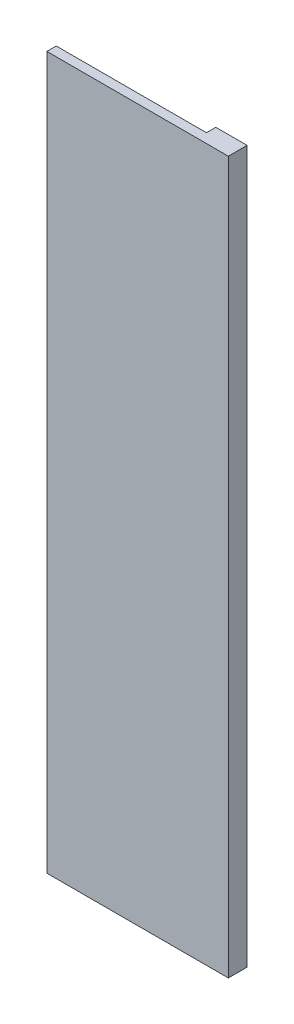
SolidWorks part; units mm, degrees
ref_plane "Front Plane" through (0, 0, 0) normal (0, 0, 1) x (1, 0, 0)
ref_plane "Top Plane" through (0, 0, 0) normal (0, 1, 0) x (1, 0, 0)
ref_plane "Right Plane" through (0, 0, 0) normal (1, 0, 0) x (0, 0, -1)
sketch "Sketch1" plane through (0, 0, 0) normal (0, 0, 1) x (1, 0, 0)
  line L0 (-48, 0) -> (48, 0) construction
  line L1 (-48, 435) -> (68, 435)
  line L2 (-48, 435) -> (-48, -20)
  line L3 (-48, -20) -> (68, -20)
  line L4 (68, 435) -> (68, -20)
  line L5 (48, 435) -> (48, 0) construction
  line L7 (48, 435) -> (-48, 435)
  line L8 (48, 435) -> (48, 0)
  line L9 (48, 0) -> (-48, 0)
  line L10 (-48, 435) -> (-48, 0)
  dimension "D1" = 20
  dimension "D2" = 20
extrude "Boss-Extrude1" add sketch "Sketch1" against normal blind 6 contours L8 L9 L2 L3 L4 L1
sketch "Sketch2" plane through (0, 0, 0) normal (0, 0, 1) x (1, 0, 0)
  line L1 (68, -20) -> (-48, -20)
  line L2 (68, -20) -> (68, 435)
  line L3 (68, 435) -> (-48, 435)
  line L4 (-48, -20) -> (-48, 435)
extrude "Boss-Extrude2" add sketch "Sketch2" along normal blind 6
sketch "Sketch3" plane through (0, 0, -6) normal (0, 0, -1) x (-1, 0, 0)
  circle A0 centre (-48, 0) radius 10
  dimension "D1" = 20
extrude "Cut-Extrude1" cut sketch "Sketch3" against normal up to surface (6 mm away) up to face at (0, 217.5, 0)
